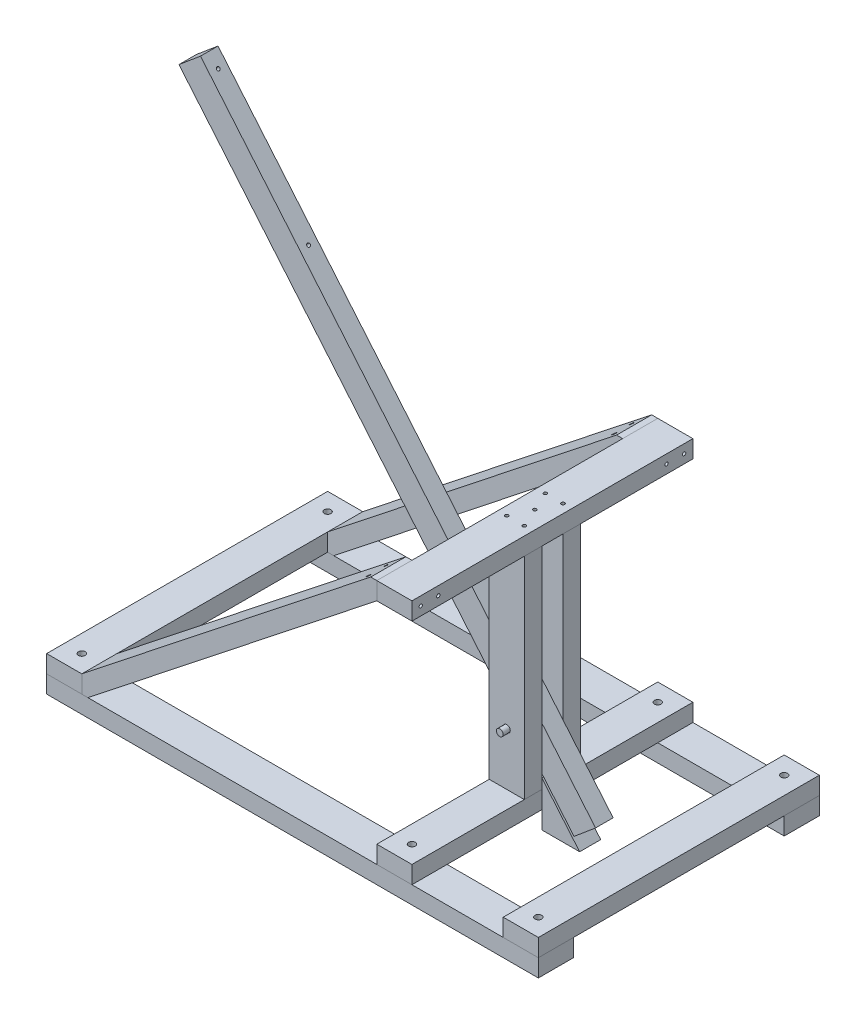
SolidWorks part; units mm, degrees
material "Pino"
ref_plane "Alzado" through (0, 0, 0) normal (0, 0, 1) x (1, 0, 0)
ref_plane "Planta" through (0, 0, 0) normal (0, 1, 0) x (1, 0, 0)
ref_plane "Vista lateral" through (0, 0, 0) normal (1, 0, 0) x (0, 0, -1)
sketch "Croquis2" plane through (0, 0, 0) normal (0, 1, 0) x (1, 0, 0)
  line L0 (-350, 200) -> (-350, 150)
  line L1 (-350, -200) -> (350, -200)
  line L2 (-350, -200) -> (-350, 200) construction
  line L3 (-350, 200) -> (350, 200)
  line L4 (350, -200) -> (350, 200) construction
  line L5 (-350, -200) -> (350, 200) construction
  line L6 (-350, 200) -> (350, -200) construction
  line L7 (-350, 150) -> (350, 150)
  line L8 (350, 150) -> (350, 200)
  line L9 (-350, -200) -> (-350, -150)
  line L10 (-350, -150) -> (350, -150)
  line L11 (350, -150) -> (350, -200)
  point P0 (0, 0)
  dimension "D1" = 400
  dimension "D2" = 700
  dimension "D3" = 50
extrude "Saliente-Extruir1" add sketch "Croquis2" along normal blind 25
sketch "Croquis3" plane through (0, 25, 0) normal (0, 1, 0) x (1, 0, 0)
  line L0 (-350, -200) -> (350, -200) construction
  line L1 (-350, 200) -> (-300, 200)
  line L2 (-350, 200) -> (-350, -200)
  line L3 (-350, -200) -> (-300, -200)
  line L4 (-300, 200) -> (-300, -200)
  line L5 (0, 200) -> (0, -200) construction
  line L6 (350, 200) -> (300, 200)
  line L7 (350, 200) -> (350, -200)
  line L8 (350, -200) -> (300, -200)
  line L9 (300, 200) -> (300, -200)
  line L10 (350, 200) -> (-350, 200) construction
  line L12 (120, 200) -> (170, 200)
  line L13 (120, 200) -> (120, -200)
  line L14 (120, -200) -> (170, -200)
  line L15 (170, 200) -> (170, -200)
  dimension "D1" = 50
  dimension "D2" = 120
extrude "Saliente-Extruir2" add sketch "Croquis3" along normal blind 25 separate body
sketch "Croquis5" plane through (0, 50, 0) normal (0, 1, 0) x (1, 0, 0)
  line L0 (120, 0) -> (170, 0) construction
  line L1 (120, 200) -> (120, -200) construction
  line L2 (170, -200) -> (170, 200) construction
  line L3 (120, 15) -> (120, 40)
  line L4 (120, 15) -> (170, 15)
  line L5 (120, 15) -> (120, -15) construction
  line L6 (120, -15) -> (170, -15)
  line L7 (170, 15) -> (170, -15) construction
  line L8 (120, 40) -> (170, 40)
  line L9 (170, 40) -> (170, 15)
  line L10 (170, -15) -> (170, -40)
  line L11 (170, -40) -> (120, -40)
  line L12 (120, -40) -> (120, -15)
  dimension "D1" = 30
  dimension "D2" = 25
extrude "Saliente-Extruir3" add sketch "Croquis5" along normal blind 300 separate body
sketch "Croquis6" plane through (0, 350, 0) normal (0, 1, 0) x (1, 0, 0)
  line L4 (120, 200) -> (120, -200)
  line L5 (120, -200) -> (170, -200)
  line L6 (170, -200) -> (170, 200)
  line L7 (170, 200) -> (120, 200)
  line L8 (120, 200) -> (120, -200)
  line L9 (120, -200) -> (170, -200)
  line L10 (170, -200) -> (170, 200)
  line L11 (170, 200) -> (120, 200)
  dimension "D1" = 0
extrude "Saliente-Extruir4" add sketch "Croquis6" along normal blind 25 separate body
sketch "Croquis7" plane through (0, 0, 200) normal (0, 0, 1) x (1, 0, 0)
  line L0 (-300, 18.1377) -> (-300, 50) construction
  line L1 (-300, 50) -> (120, 381.8623) construction
  line L2 (120, 381.8623) -> (120, 350) construction
  line L4 (120, 350) -> (-300, 18.1377) construction
  line L6 (120, 350) -> (120, 375) construction
  line L7 (-300, 25) -> (-300, 50) construction
  line L9 (-300, 50) -> (-300, 25)
  line L10 (-300, 25) -> (-291.3151, 25)
  line L11 (-291.3151, 25) -> (120, 350)
  line L12 (120, 350) -> (120, 375)
  line L13 (120, 375) -> (111.3151, 375)
  line L14 (111.3151, 375) -> (-300, 50)
  dimension "D1" = 25
extrude "Saliente-Extruir5" add sketch "Croquis7" against normal blind 50 separate body
mirror "Simetría2" about plane through (0, 0, 0) normal (0, 0, 1) of bodies 109
sketch "Croquis8" plane through (0, 0, 0) normal (0, 0, 1) x (1, 0, 0)
  line L0 (145, 25) -> (145, 375) construction
  line L1 (120, 25) -> (170, 25) construction
  line L2 (120, 375) -> (170, 375) construction
  line L3 (120, 125) -> (170, 125) construction
  line L4 (120, 350) -> (120, 50) construction
  line L5 (170, 350) -> (170, 50) construction
  line L6 (145, 125) -> (-333.8768, 695.7031) construction
  line L7 (145, 125) -> (228.6115, 25.3558) construction
  line L8 (-350, 25) -> (350, 25) construction
  line L9 (-318.5559, 708.5589) -> (-349.1977, 682.8474) construction
  line L10 (-349.1977, 682.8474) -> (213.2906, 12.5) construction
  line L11 (213.2906, 12.5) -> (243.9323, 38.2115) construction
  line L12 (243.9323, 38.2115) -> (-318.5559, 708.5589) construction
  line L13 (350, 12.5) -> (-350, 12.5) construction
  line L14 (350, 25) -> (350, 0) construction
  line L15 (-350, 25) -> (-350, 0) construction
  line L16 (170, 64.0917) -> (223.7793, 0)
  line L17 (-350, 0) -> (350, 0) construction
  line L18 (170, 64.0917) -> (170, 0)
  line L19 (170, 0) -> (223.7793, 0)
  line L20 (120, 125) -> (-600, 125) construction
  arc A0 (-333.8768, 695.7031) -> (-600, 125) centre (145, 125) ccw construction
  dimension "D1" = 100
  dimension "D2" = 50
  dimension "D3" = 40
  dimension "D4" = 950
  dimension "D5" = 708.5589
extrude "Saliente-Extruir6" add sketch "Croquis8" along normal blind 15 and the other way blind 15 separate body
sketch "Croquis9" plane through (0, 0, 0) normal (0, 0, 1) x (1, 0, 0)
  line L0 (-349.1977, 682.8474) -> (-318.5559, 708.5589)
  line L1 (-318.5559, 708.5589) -> (243.9323, 38.2115)
  line L2 (243.9323, 38.2115) -> (213.2906, 12.5)
  line L3 (213.2906, 12.5) -> (-349.1977, 682.8474)
  circle A0 centre (145, 125) radius 5
  dimension "D1" = 10
extrude "Saliente-Extruir7" add sketch "Croquis9" along normal blind 12.5 and the other way blind 12.5 separate body
sketch "Croquis10" plane through (0, 0, 40) normal (0, 0, 1) x (1, 0, 0)
  line L0 (120, 125) -> (170, 125) construction
  circle A0 centre (145, 125) radius 5
  dimension "D1" = 10
extrude "Cortar-Extruir1" cut sketch "Croquis10" against normal up to surface (80 mm away) up to face at (145, 200, -40)
sketch "Croquis11" plane through (0, 0, 0) normal (0, 0, 1) x (1, 0, 0)
  circle A0 centre (145, 125) radius 4.7625
  dimension "D1" = 9.525
extrude "Saliente-Extruir8" add sketch "Croquis11" along normal offset from surface 10 and the other way offset from surface (52.5 mm away) 12.5 separate body up to face at (150, 125, 40) offset beyond the face yes other way up to face at (150, 125, -40)
sketch "Croquis12" plane through (0, 50, 0) normal (0, 1, 0) x (1, 0, 0)
  line L0 (350, 150) -> (350, 200) construction
  line L1 (350, 175) -> (-350, 175) construction
  line L2 (-350, 200) -> (-350, -200) construction
  line L3 (-325, 200) -> (-325, -200) construction
  line L4 (-300, 200) -> (-350, 200) construction
  line L5 (-350, -200) -> (-300, -200) construction
  line L6 (350, -150) -> (350, -200) construction
  line L7 (350, -175) -> (-350, -175) construction
  line L8 (325, -200) -> (325, 200) construction
  line L9 (300, -200) -> (350, -200) construction
  line L10 (350, 200) -> (300, 200) construction
  line L11 (145, 200) -> (145, -200) construction
  line L12 (170, 200) -> (120, 200) construction
  line L13 (120, -200) -> (170, -200) construction
  circle A0 centre (-325, 175) radius 4.7625
  circle A1 centre (-325, -175) radius 4.7625
  circle A2 centre (325, -175) radius 4.7625
  circle A3 centre (325, 175) radius 4.7625
  circle A4 centre (145, 175) radius 4.7625
  circle A5 centre (145, -175) radius 4.7625
  dimension "D1" = 9.525
extrude "Cortar-Extruir2" cut sketch "Croquis12" against normal up to surface (50 mm away) up to face at (0, 0, 175)
sketch "Croquis13" plane through (170, 0, 0) normal (1, 0, 0) x (0, 0, -1)
  line L0 (-200, 362.5) -> (200, 362.5) construction
  line L1 (-200, 375) -> (-200, 350) construction
  line L2 (200, 375) -> (200, 350) construction
  line L3 (150, 350) -> (200, 350) construction
  line L4 (175, 350) -> (175, 375) construction
  line L5 (-200, 375) -> (200, 375) construction
  line L6 (0, 350) -> (0, 375) construction
  line L7 (-200, 350) -> (200, 350) construction
  circle A0 centre (162.5, 362.5) radius 2.3813
  circle A1 centre (187.5, 362.5) radius 2.3813
  circle A2 centre (-187.5, 362.5) radius 2.3813
  circle A3 centre (-162.5, 362.5) radius 2.3813
  dimension "D1" = 4.7625
  dimension "D2" = 12.5
  dimension "D3" = 12.5
extrude "Cortar-Extruir3" cut sketch "Croquis13" against normal up to surface (74.5047 mm away)
sketch "Croquis14" plane through (-350, 0, 0) normal (-1, 0, 0) x (0, 0, 1)
  line L0 (-200, 37.5) -> (200, 37.5) construction
  line L1 (-200, 50) -> (-200, 25) construction
  line L2 (200, 50) -> (200, 25) construction
  line L3 (175, 0) -> (175, 50) construction
  line L4 (150, 0) -> (200, 0) construction
  line L5 (-200, 50) -> (200, 50) construction
  line L6 (0, 25) -> (0, 50) construction
  line L7 (-200, 25) -> (200, 25) construction
  circle A0 centre (187.5, 37.5) radius 2.3813
  circle A1 centre (162.5, 37.5) radius 2.3813
  circle A2 centre (-187.5, 37.5) radius 2.3813
  circle A3 centre (-162.5, 37.5) radius 2.3813
  dimension "D2" = 4.7625
  dimension "D1" = 12.5
  dimension "D3" = 12.5
extrude "Cortar-Extruir4" cut sketch "Croquis14" against normal up to surface (74.5047 mm away)
sketch "Croquis15" plane through (120, 0, 0) normal (-1, 0, 0) x (0, 0, 1)
  line L0 (-200, 37.5) -> (200, 37.5) construction
  line L1 (-200, 50) -> (-200, 25) construction
  line L2 (200, 50) -> (200, 25) construction
  line L3 (0, 0) -> (0, 64.0917) construction
  line L4 (-15, 64.0917) -> (15, 64.0917) construction
  circle A0 centre (-7.5, 37.5) radius 2.3812
  circle A1 centre (7.5, 37.5) radius 2.3812
  dimension "D2" = 7.5
  dimension "D3" = 4.7625
  dimension "D1" = 7.5
extrude "Cortar-Extruir5" cut sketch "Croquis15" against normal up to surface (72.3131 mm away)
sketch "Croquis16" plane through (161.9609, 135.9013, 0) normal (0.766, 0.6428, 0) x (0, 0, -1)
  line L0 (0, 747.5514) -> (0, -127.525) construction
  line L1 (12.5, 747.5514) -> (-12.5, 747.5514) construction
  line L2 (12.5, -127.525) -> (-12.5, -127.525) construction
  circle A0 centre (0, 727.5514) radius 2.3813
  circle A1 centre (0, 527.5514) radius 2.3813
  dimension "D1" = 20
  dimension "D2" = 200
  dimension "D3" = 4.7625
extrude "Cortar-Extruir6" cut sketch "Croquis16" against normal up to surface (40 mm away) up to face at (-67.9535, 347.6737, 0)
sketch "Croquis17" plane through (0, 25, 0) normal (0, -1, 0) x (1, 0, 0)
  line L0 (120, 0) -> (170, 0) construction
  line L1 (120, -200) -> (120, 200) construction
  line L2 (170, -15) -> (170, 15) construction
  line L3 (120, 15) -> (120, 40) construction
  line L4 (120, 27.5) -> (170, 27.5) construction
  line L5 (170, 200) -> (170, -200) construction
  line L6 (120, -15) -> (120, -40) construction
  line L7 (120, -27.5) -> (170, -27.5) construction
  line L8 (145, 0) -> (145, 40) construction
  line L9 (120, 40) -> (170, 40) construction
  line L10 (145, 0) -> (145, -27.5) construction
  circle A0 centre (132.5, 27.5) radius 2.3813
  circle A1 centre (157.5, 27.5) radius 2.3813
  circle A2 centre (132.5, -27.5) radius 2.3813
  circle A3 centre (157.5, -27.5) radius 2.3813
  dimension "D3" = 4.7625
  dimension "D1" = 12.5
  dimension "D2" = 12.5
extrude "Cortar-Extruir7" cut sketch "Croquis17" against normal blind 70
sketch "Croquis18" plane through (0, 375, 0) normal (0, 1, 0) x (1, 0, 0)
  line L0 (145, 200) -> (145, -200) construction
  line L1 (170, 200) -> (120, 200) construction
  line L2 (120, -200) -> (170, -200) construction
  circle A0 centre (132.5, -27.5) radius 2.3813 construction
  circle A1 centre (157.5, -27.5) radius 2.3813 construction
  circle A2 centre (132.5, 27.5) radius 2.3813 construction
  circle A3 centre (157.5, 27.5) radius 2.3813 construction
  circle A4 centre (132.5, -27.5) radius 2.3813
  circle A5 centre (157.5, -27.5) radius 2.3813
  circle A6 centre (132.5, 27.5) radius 2.3813
  circle A7 centre (157.5, 27.5) radius 2.3813
  circle A8 centre (145, 0) radius 2.3813
extrude "Cortar-Extruir8" cut sketch "Croquis18" against normal blind 70
